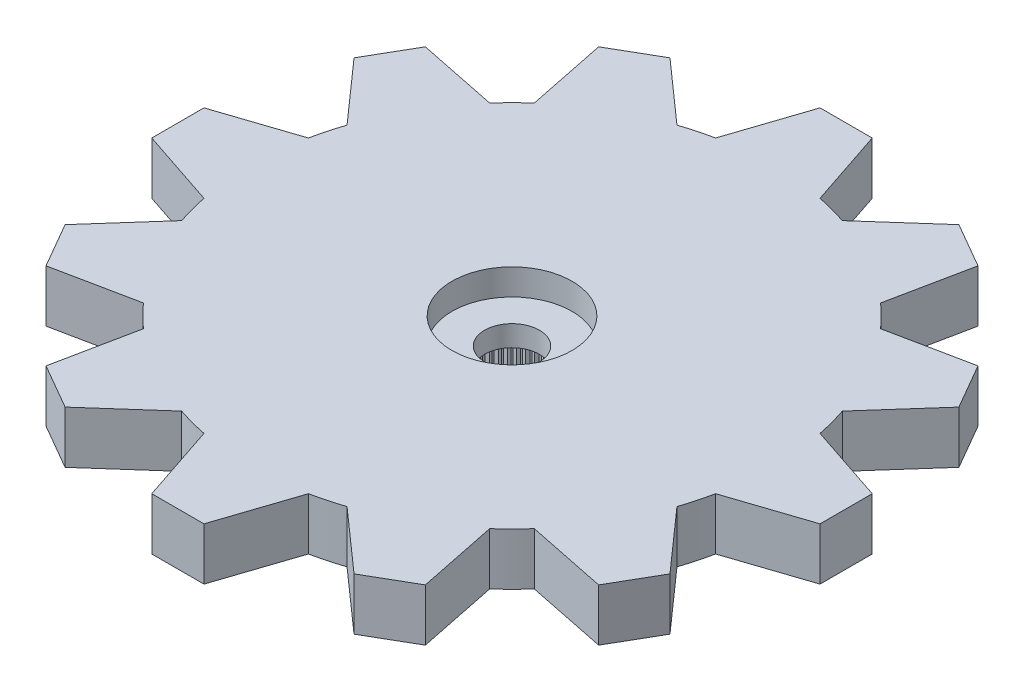
SolidWorks part; units mm, degrees
material "PVC Rígido"
ref_plane "Plano frontal" through (0, 0, 0) normal (0, 0, 1) x (1, 0, 0)
ref_plane "Plano superior" through (0, 0, 0) normal (0, 1, 0) x (1, 0, 0)
ref_plane "Plano direito" through (0, 0, 0) normal (1, 0, 0) x (0, 0, -1)
sketch "Esboço1" plane through (0, 0, 0) normal (0, 1, 0) x (1, 0, 0)
  line L0 (0, 0) -> (-14.05, 0) construction
  line L1 (-14.1591, 1.997) -> (-2.2091, 2.65)
  line L2 (-2.2091, -2.65) -> (-14.1591, -1.997)
  arc A0 (-2.2091, -2.65) -> (-2.2091, 2.65) centre (0, 0) ccw
  arc A1 (-14.1591, 1.997) -> (-14.1591, -1.997) centre (-14.05, 0) ccw
  dimension "D1" = 6.9
  dimension "D2" = 4
  dimension "D3" = 19.5
  dimension "D4" = 5.3
extrude "Ressalto-extrusão1" add sketch "Esboço1" against normal blind 1.4
sketch "Esboço2" plane through (0, -1.4, 0) normal (0, -1, 0) x (1, 0, 0)
  arc A0 (-2.2091, -2.65) -> (-2.2091, 2.65) centre (0, 0) ccw construction
  circle A1 centre (0, 0) radius 3.45
extrude "Ressalto-extrusão2" add sketch "Esboço2" along normal offset from surface (2.4 mm away) 3.8 up to face at (-7.242, 0, 0)
hole_wizard "Furo4" positions "Esboço9" profile "Esboço10" legacy end condition through all
sketch "Esboço9" plane through (0, 0, 0) normal (0, 1, 0) x (1, 0, 0)
  line L1 (-14.45, 0) -> (0, 0) construction
  arc A2 (-14.1591, 1.997) -> (-14.1591, -1.997) centre (-14.05, 0) ccw construction
  point P0 (-14.45, 0)
  point P19 (-16.05, 0)
  dimension "D1" = 1.6
sketch "Esboço10" plane through (-14.45, 0, 0) normal (1, 0, 0) x (0, 0, 1)
  line L0 (0, 0) -> (0, 3.8)
  line L1 (0, 3.8) -> (0.6, 3.8)
  line L2 (0.6, 3.8) -> (0.6, 0)
  line L3 (0.6, 0) -> (0, 0)
  line L4 (0, 110) -> (0, -10) construction
  dimension "Diameter" = 1.2
  dimension "Depth" = 3.8
pattern_linear "Padrão linear1" count 6 spacing 2 along (1, 0, 0) of "Furo4"
pattern_circular "PadrãoCircular2" count 2 over 360 about axis through (0, 0, 0) along (0, 1, 0) of "Ressalto-extrusão1", "Furo4", "Padrão linear1"
hole_wizard "Furo1" positions "Esboço3" profile "Esboço4" legacy
sketch "Esboço3" plane through (0, -3.8, 0) normal (0, -1, 0) x (-1, 0, 0)
  point P0 (0, 0)
sketch "Esboço4" plane through (0, -3.8, 0) normal (1, 0, 0) x (0, 0, -1)
  line L0 (0, 0) -> (0, 2)
  line L1 (0, 2) -> (2.475, 2)
  line L2 (2.475, 2) -> (2.475, 0)
  line L3 (2.475, 0) -> (0, 0)
  line L4 (0, 110) -> (0, -10) construction
  dimension "Diameter" = 4.95
  dimension "Depth" = 2
hole_wizard "Furo2" positions "Esboço5" profile "Esboço6" legacy
sketch "Esboço5" plane through (0, 0, 0) normal (0, 1, 0) x (1, 0, 0)
  point P0 (0, 0)
sketch "Esboço6" plane through (0, 0, 0) normal (1, 0, 0) x (0, 0, 1)
  line L0 (0, 0) -> (0, 1)
  line L1 (0, 1) -> (2.3, 1)
  line L2 (2.3, 1) -> (2.3, 0)
  line L3 (2.3, 0) -> (0, 0)
  line L4 (0, 110) -> (0, -10) construction
  dimension "Diameter" = 4.6
  dimension "Depth" = 1
hole_wizard "Furo3" positions "Esboço7" profile "Esboço8" legacy end condition through all
sketch "Esboço7" plane through (0, 0, 0) normal (0, 1, 0) x (1, 0, 0)
  point P0 (0, 0)
sketch "Esboço8" plane through (0, 0, 0) normal (1, 0, 0) x (0, 0, 1)
  line L0 (0, 0) -> (0, 3.8)
  line L1 (0, 3.8) -> (1.05, 3.8)
  line L2 (1.05, 3.8) -> (1.05, 0)
  line L3 (1.05, 0) -> (0, 0)
  line L4 (0, 110) -> (0, -10) construction
  dimension "Diameter" = 2.1
  dimension "Depth" = 3.8
sketch "Esboço11" plane through (0, -3.8, 0) normal (0, -1, 0) x (1, 0, 0)
  line L0 (-0.0981, 2.4731) -> (0, 2.375)
  line L1 (0, 2.375) -> (0.0981, 2.4731)
  line L2 (0, 0) -> (0, 2.475) construction
  circle A0 centre (0, 0) radius 2.375 construction
  circle A1 centre (0, 0) radius 2.475
  arc A2 (0.0981, 2.4731) -> (-0.0981, 2.4731) centre (0, 0) ccw
  dimension "D3" = 4.75
  dimension "D2" = 0.1
  dimension "D1" = 0
extrude "Ressalto-extrusão3" add sketch "Esboço11" against normal up to surface (2 mm away) up to face at (0, -1.8, 1.05)
pattern_circular "PadrãoCircular1" count 60 over 360 about axis through (0, 0, 0) along (0, 1, 0) of "Ressalto-extrusão3"
sketch "Sketch2" plane through (0, -3.8, 0) normal (0, -1, 0) x (1, 0, 0)
  line L1 (-16.5, -8.5) -> (16.5, -8.5)
  line L2 (-16.5, -8.5) -> (-16.5, 8.5)
  line L3 (-16.5, 8.5) -> (16.5, 8.5)
  line L4 (16.5, -8.5) -> (16.5, 8.5)
  line L5 (-16.5, -8.5) -> (16.5, 8.5) construction
  line L6 (-16.5, 8.5) -> (16.5, -8.5) construction
  circle A0 centre (0, 0) radius 3.45
  dimension "D1" = 6.9
  dimension "D2" = 33
  dimension "D3" = 17
extrude "Cut-Extrude1" cut sketch "Sketch2" against normal blind 10
sketch "Sketch3" plane through (0, 0, 0) normal (0, 1, 0) x (1, 0, 0)
  circle A0 centre (0, 0) radius 3.45
  circle A1 centre (0, 0) radius 10
  dimension "D1" = 6.9
  dimension "D2" = 20
extrude "Boss-Extrude1" add sketch "Sketch3" against normal blind 2
sketch "Sketch5" plane through (0, 0, 0) normal (0, 1, 0) x (1, 0, 0)
  line L0 (0, 15) -> (0, -15) construction
  line L1 (-2, 9.798) -> (2, 9.798)
  line L2 (2, 9.798) -> (1, 12.798)
  line L3 (1, 12.798) -> (-1, 12.798)
  line L4 (-1, 12.798) -> (-2, 9.798)
  line L5 (5.533, 11.5834) -> (3.1669, 9.4853)
  line L6 (3.1669, 9.4853) -> (6.631, 7.4853)
  line L7 (6.631, 7.4853) -> (7.265, 10.5834)
  line L8 (7.265, 10.5834) -> (5.533, 11.5834)
  line L9 (10.5834, 7.265) -> (7.4853, 6.631)
  line L10 (7.4853, 6.631) -> (9.4853, 3.1669)
  line L11 (9.4853, 3.1669) -> (11.5834, 5.533)
  line L12 (11.5834, 5.533) -> (10.5834, 7.265)
  line L13 (12.798, 1) -> (9.798, 2)
  line L14 (9.798, 2) -> (9.798, -2)
  line L15 (9.798, -2) -> (12.798, -1)
  line L16 (12.798, -1) -> (12.798, 1)
  line L17 (11.5834, -5.533) -> (9.4853, -3.1669)
  line L18 (9.4853, -3.1669) -> (7.4853, -6.631)
  line L19 (7.4853, -6.631) -> (10.5834, -7.265)
  line L20 (10.5834, -7.265) -> (11.5834, -5.533)
  line L21 (7.265, -10.5834) -> (6.631, -7.4853)
  line L22 (6.631, -7.4853) -> (3.1669, -9.4853)
  line L23 (3.1669, -9.4853) -> (5.533, -11.5834)
  line L24 (5.533, -11.5834) -> (7.265, -10.5834)
  line L25 (1, -12.798) -> (2, -9.798)
  line L26 (2, -9.798) -> (-2, -9.798)
  line L27 (-2, -9.798) -> (-1, -12.798)
  line L28 (-1, -12.798) -> (1, -12.798)
  line L29 (-5.533, -11.5834) -> (-3.1669, -9.4853)
  line L30 (-3.1669, -9.4853) -> (-6.631, -7.4853)
  line L31 (-6.631, -7.4853) -> (-7.265, -10.5834)
  line L32 (-7.265, -10.5834) -> (-5.533, -11.5834)
  line L33 (-10.5834, -7.265) -> (-7.4853, -6.631)
  line L34 (-7.4853, -6.631) -> (-9.4853, -3.1669)
  line L35 (-9.4853, -3.1669) -> (-11.5834, -5.533)
  line L36 (-11.5834, -5.533) -> (-10.5834, -7.265)
  line L37 (-12.798, -1) -> (-9.798, -2)
  line L38 (-9.798, -2) -> (-9.798, 2)
  line L39 (-9.798, 2) -> (-12.798, 1)
  line L40 (-12.798, 1) -> (-12.798, -1)
  line L41 (-11.5834, 5.533) -> (-9.4853, 3.1669)
  line L42 (-9.4853, 3.1669) -> (-7.4853, 6.631)
  line L43 (-7.4853, 6.631) -> (-10.5834, 7.265)
  line L44 (-10.5834, 7.265) -> (-11.5834, 5.533)
  line L45 (-7.265, 10.5834) -> (-6.631, 7.4853)
  line L46 (-6.631, 7.4853) -> (-3.1669, 9.4853)
  line L47 (-3.1669, 9.4853) -> (-5.533, 11.5834)
  line L48 (-5.533, 11.5834) -> (-7.265, 10.5834)
  circle A0 centre (0, 0) radius 10 construction
  point P5 (0, 9.798)
  point P8 (0, 12.798)
  point P13 (0, 0)
  point P58 (0, 0)
  dimension "D1" = 4
  dimension "D2" = 2
  dimension "D3" = 3
  dimension "D4" = 30
  dimension "D5" = 12
extrude "Boss-Extrude2" add sketch "Sketch5" against normal blind 2
